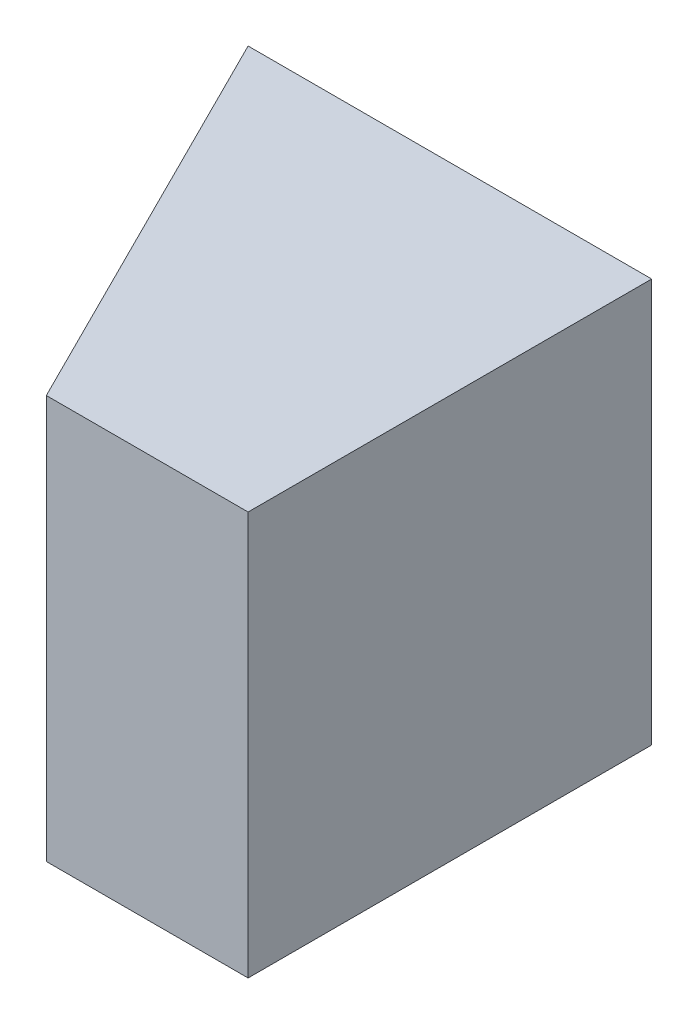
SolidWorks part; units mm, degrees
ref_plane "Front Plane" through (0, 0, 0) normal (0, 0, 1) x (1, 0, 0)
ref_plane "Top Plane" through (0, 0, 0) normal (0, 1, 0) x (1, 0, 0)
ref_plane "Right Plane" through (0, 0, 0) normal (1, 0, 0) x (0, 0, -1)
sketch "Sketch1" plane through (0, 0, 0) normal (0, 0, 1) x (1, 0, 0)
  line L1 (0, 0) -> (20, 0)
  line L2 (0, 0) -> (0, 20)
  line L3 (0, 20) -> (20, 20)
  line L4 (20, 0) -> (20, 20)
  dimension "D1" = 20
  dimension "D2" = 20
extrude "Boss-Extrude1" add sketch "Sketch1" along normal blind 20
sketch "Sketch2" plane through (0, 20, 0) normal (0, 1, 0) x (1, 0, 0)
  line L0 (0, 0) -> (10, -20)
  line L1 (20, -20) -> (0, -20) construction
  line L2 (10, -20) -> (0, -20)
  line L3 (0, -20) -> (0, 0)
extrude "Cut-Extrude1" cut sketch "Sketch2" against normal blind 20
